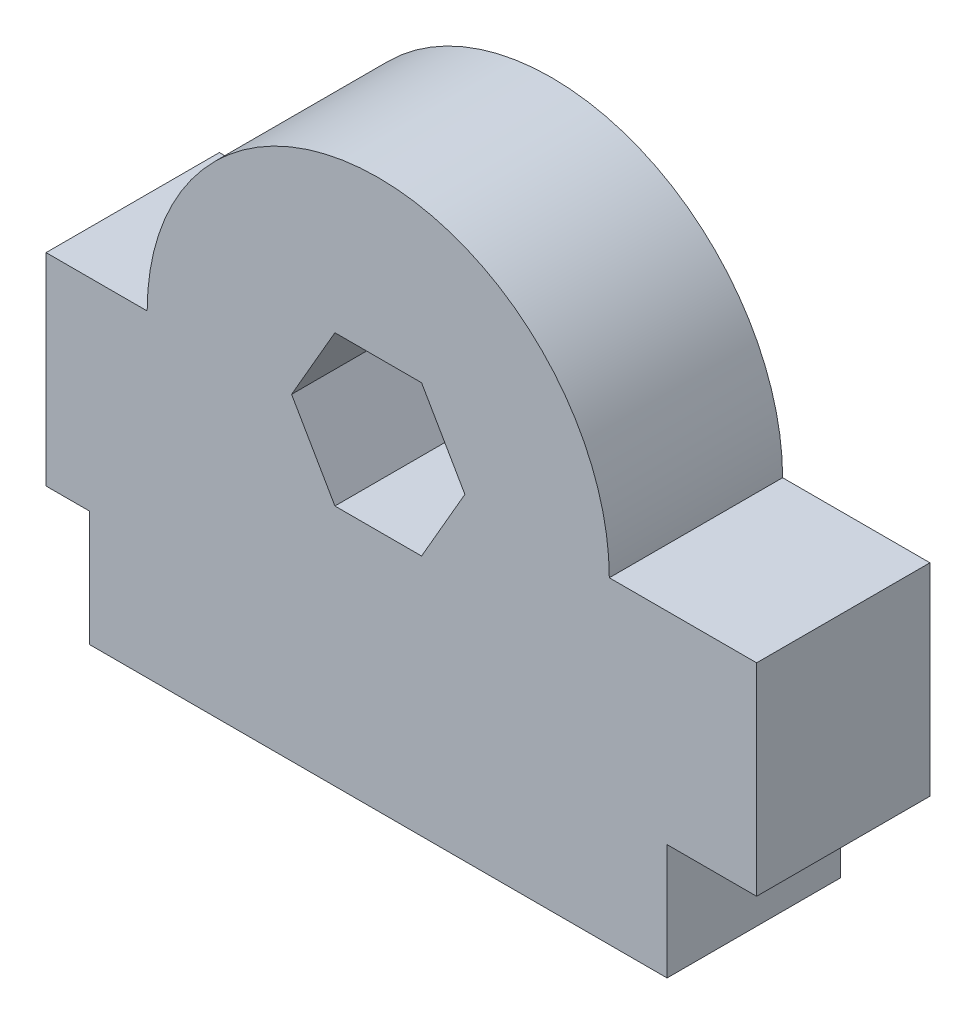
SolidWorks part; units mm, degrees
ref_plane "Front Plane" through (0, 0, 0) normal (0, 0, 1) x (1, 0, 0)
ref_plane "Top Plane" through (0, 0, 0) normal (0, 1, 0) x (1, 0, 0)
ref_plane "Right Plane" through (0, 0, 0) normal (1, 0, 0) x (0, 0, -1)
sketch "Sketch1" plane through (0, 0, 0) normal (0, 0, 1) x (1, 0, 0)
  line L0 (0, 0) -> (20, 0)
  line L1 (0, 0) -> (0, 4)
  line L2 (20, 0) -> (20, 4)
  line L3 (0, 4) -> (-1.5, 4)
  line L4 (23.1, 11) -> (23.1, 4)
  line L5 (-1.5, 4) -> (-1.5, 11)
  line L6 (-1.5, 11) -> (2, 11)
  line L7 (18, 11) -> (23.1, 11)
  line L8 (23.1, 4) -> (20, 4)
  line L11 (13, 11) -> (11.5, 13.5981)
  line L12 (11.5, 13.5981) -> (8.5, 13.5981)
  line L13 (8.5, 13.5981) -> (7, 11)
  line L14 (7, 11) -> (8.5, 8.4019)
  line L15 (8.5, 8.4019) -> (11.5, 8.4019)
  line L16 (11.5, 8.4019) -> (13, 11)
  arc A0 (18, 11) -> (2, 11) centre (10, 11) ccw
  dimension "D1" = 8
  dimension "D5" = 11.5
  dimension "D6" = 20
  dimension "D2" = 7
  dimension "D3" = 8.5
  dimension "D4" = 10
  dimension "D7" = 23.1
  dimension "D8" = 1.5
  dimension "D9" = 4
  dimension "D10" = 8.4019
extrude "Boss-Extrude1" add sketch "Sketch1" along normal blind 6
